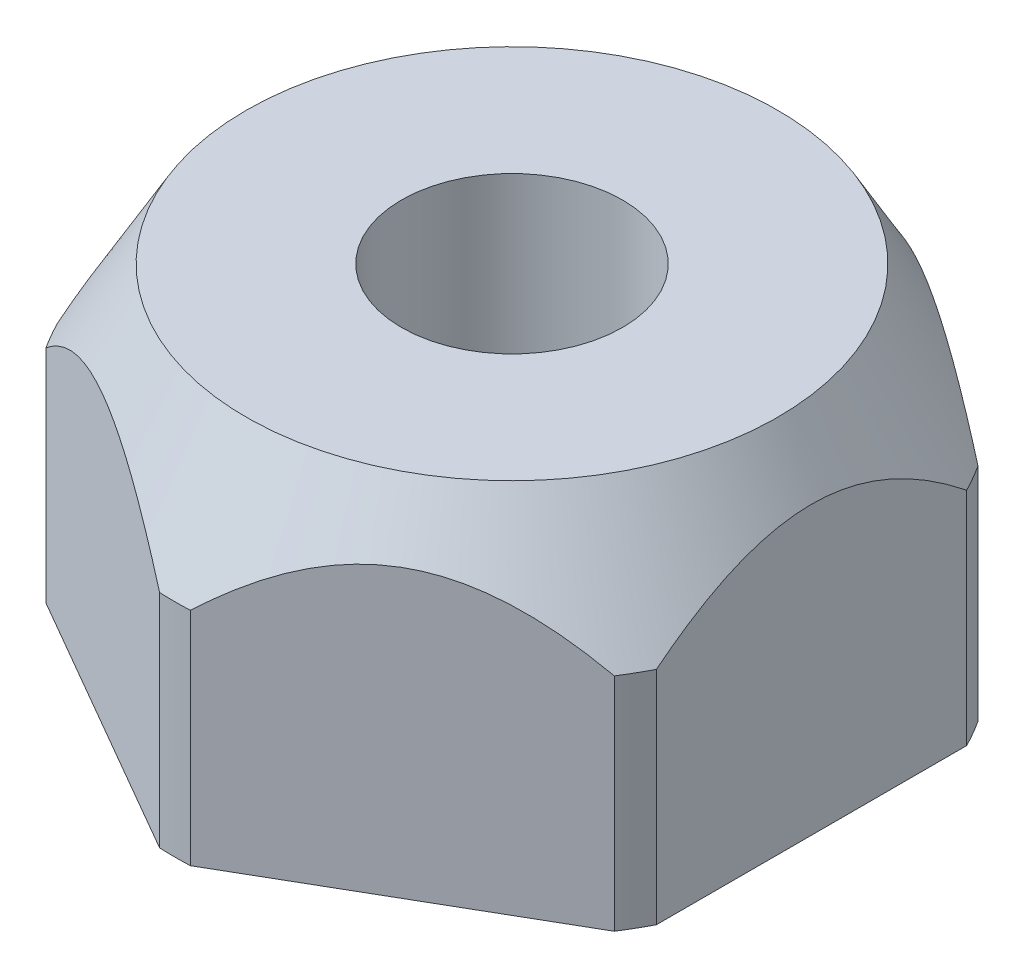
SolidWorks part; units mm, degrees
material "AISI 316 Stainless Steel Sheet (SS)"
ref_plane "Front" through (0, 0, 0) normal (0, 0, 1) x (1, 0, 0)
ref_plane "Top" through (0, 0, 0) normal (0, 1, 0) x (1, 0, 0)
ref_plane "Right" through (0, 0, 0) normal (1, 0, 0) x (0, 0, -1)
sketch "Sketch1" plane through (0, 0, 0) normal (0, 0, 1) x (1, 0, 0)
  line L0 (-1.4478, 0) -> (-4.4196, 0)
  line L1 (-4.4196, 0) -> (-4.4196, 2.8976)
  line L2 (-4.4196, 2.8976) -> (-3.4822, 4.5212)
  line L3 (-3.4822, 4.5212) -> (-1.4478, 4.5212)
  line L4 (0, 4.5212) -> (0, 0) construction
  line L5 (-1.4478, 4.5212) -> (-1.4478, 0)
  dimension "D1" = 4.4196
  dimension "D2" = 4.5212
  dimension "D3" = 30
  dimension "D4" = 1.4478
revolve "Revolve1" add sketch "Sketch1" angle 360 about L4
sketch "Sketch2" plane through (0, 0, 0) normal (0, 1, 0) x (1, 0, 0)
  line L1 (0, 4.5314) -> (-3.9243, 2.2657)
  line L2 (-3.9243, 2.2657) -> (-3.9243, -2.2657)
  line L3 (-3.9243, -2.2657) -> (0, -4.5314)
  line L4 (0, -4.5314) -> (3.9243, -2.2657)
  line L5 (3.9243, -2.2657) -> (3.9243, 2.2657)
  line L6 (3.9243, 2.2657) -> (0, 4.5314)
  circle A0 centre (0, 0) radius 3.9243 construction
  circle A1 centre (0, 0) radius 8.337
  dimension "D1" = 7.8486
extrude "Extrude1" cut sketch "Sketch2" along normal through all
